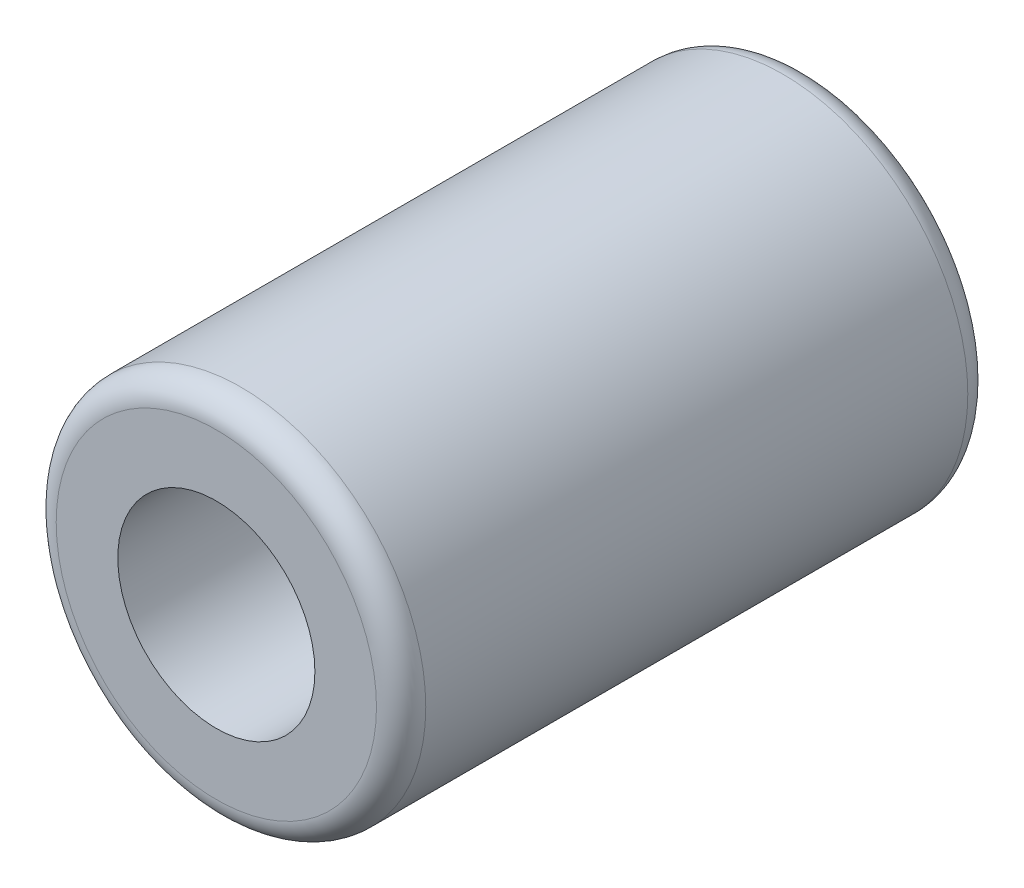
SolidWorks part; units mm, degrees
ref_plane "Front Plane" through (0, 0, 0) normal (0, 0, 1) x (1, 0, 0)
ref_plane "Top Plane" through (0, 0, 0) normal (0, 1, 0) x (1, 0, 0)
ref_plane "Right Plane" through (0, 0, 0) normal (1, 0, 0) x (0, 0, -1)
sketch "Sketch1" plane through (0, 0, 0) normal (0, 0, 1) x (1, 0, 0)
  circle A0 centre (0, 0) radius 7.5
  circle A1 centre (0, 0) radius 4
  dimension "D1" = 15
  dimension "D2" = 8
extrude "Boss-Extrude1" add sketch "Sketch1" along normal blind 24
fillet "Fillet2" radius 1 2 edges at (7.5, 0, 0) (7.5, 0, 24)
